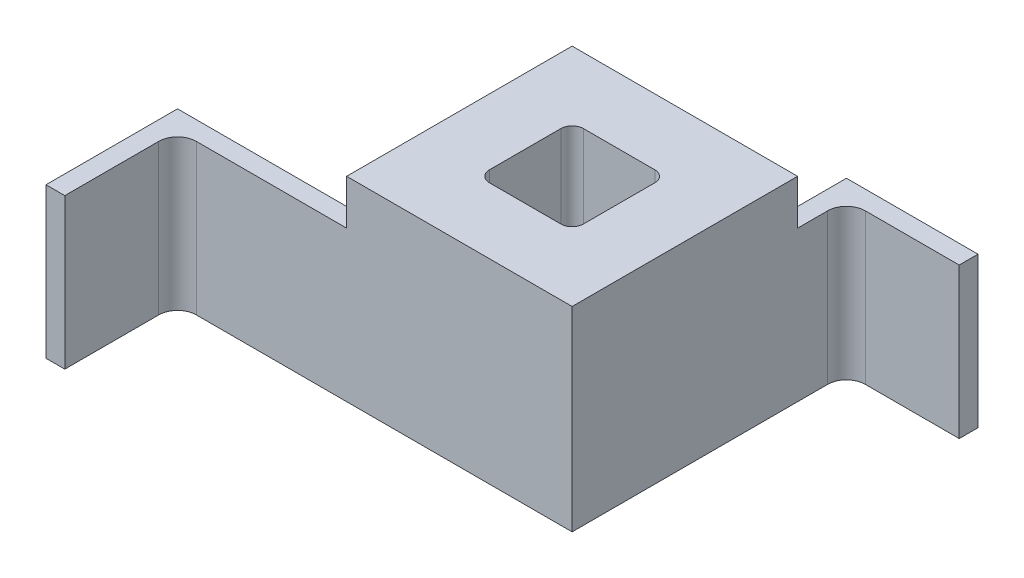
SolidWorks part; units mm, degrees
ref_plane "Front Plane" through (0, 0, 0) normal (0, 0, 1) x (1, 0, 0)
ref_plane "Top Plane" through (0, 0, 0) normal (0, 1, 0) x (1, 0, 0)
ref_plane "Right Plane" through (0, 0, 0) normal (1, 0, 0) x (0, 0, -1)
sketch "Sketch1" plane through (0, 0, 0) normal (0, 1, 0) x (1, 0, 0)
  line L1 (-30, 30) -> (30, 30)
  line L2 (-30, 30) -> (-30, -30)
  line L3 (-30, -30) -> (30, -30)
  line L4 (30, 30) -> (30, -30)
  line L5 (-30, 30) -> (30, -30) construction
  line L6 (-30, -30) -> (30, 30) construction
  point P0 (0, 0)
  dimension "D1" = 60
extrude "Boss-Extrude1" add sketch "Sketch1" along normal blind 51.95
sketch "Sketch3" plane through (0, 0, -30) normal (0, 0, -1) x (-1, 0, 0)
  line L0 (-30, 0) -> (30, 0) construction
  line L1 (-30, 40) -> (-25, 40)
  line L2 (-30, 40) -> (-30, 0)
  line L3 (-30, 0) -> (-25, 0)
  line L4 (-25, 40) -> (-25, 0)
  line L5 (-30, 51.95) -> (-30, 0) construction
  dimension "D1" = 5
  dimension "D2" = 40
extrude "Boss-Extrude2" add sketch "Sketch3" along normal blind 18
sketch "Sketch4" plane through (30, 0, 0) normal (1, 0, 0) x (0, 0, -1)
  line L0 (-30, 0) -> (48, 0) construction
  line L1 (48, 40) -> (43, 40)
  line L2 (48, 40) -> (48, 0)
  line L3 (48, 0) -> (43, 0)
  line L4 (43, 40) -> (43, 0)
  line L5 (48, 40) -> (30, 40) construction
  line L6 (48, 40) -> (48, 0) construction
  dimension "D1" = 5
extrude "Boss-Extrude3" add sketch "Sketch4" along normal blind 30
sketch "Sketch5" plane through (-30, 0, 0) normal (-1, 0, 0) x (0, 0, 1)
  line L0 (-30, 0) -> (30, 0) construction
  line L1 (30, 40) -> (25, 40)
  line L2 (30, 40) -> (30, 0)
  line L3 (30, 0) -> (25, 0)
  line L4 (25, 40) -> (25, 0)
  line L5 (30, 51.95) -> (30, 0) construction
  dimension "D1" = 5
  dimension "D2" = 40
extrude "Boss-Extrude4" add sketch "Sketch5" along normal blind 50
sketch "Sketch6" plane through (0, 0, 30) normal (0, 0, 1) x (1, 0, 0)
  line L0 (-80, 0) -> (30, 0) construction
  line L1 (-80, 40) -> (-75, 40)
  line L2 (-80, 40) -> (-80, 0)
  line L3 (-80, 0) -> (-75, 0)
  line L4 (-75, 40) -> (-75, 0)
  line L5 (-80, 40) -> (-30, 40) construction
  line L6 (-80, 0) -> (-80, 40) construction
  dimension "D1" = 5
extrude "Boss-Extrude5" add sketch "Sketch6" along normal blind 30
sketch "Sketch7" plane through (0, 51.95, 0) normal (0, 1, 0) x (1, 0, 0)
  line L1 (-12.5, 12.5) -> (12.5, 12.5)
  line L2 (-12.5, 12.5) -> (-12.5, -12.5)
  line L3 (-12.5, -12.5) -> (12.5, -12.5)
  line L4 (12.5, 12.5) -> (12.5, -12.5)
  line L5 (-12.5, 12.5) -> (12.5, -12.5) construction
  line L6 (-12.5, -12.5) -> (12.5, 12.5) construction
  point P0 (0, 0)
  dimension "D1" = 25
extrude "Cut-Extrude1" cut sketch "Sketch7" against normal through all
fillet "Fillet1" radius 3 4 edges at (-12.5, 25.975, 12.5) (12.5, 25.975, 12.5) (12.5, 25.975, -12.5) (-12.5, 25.975, -12.5)
fillet "Fillet2" radius 5 2 edges at (-75, 20, 30) (30, 20, -43)
fillet "Fillet3" radius 5 2 edges at (25, 20, -30) (-30, 20, 25)
